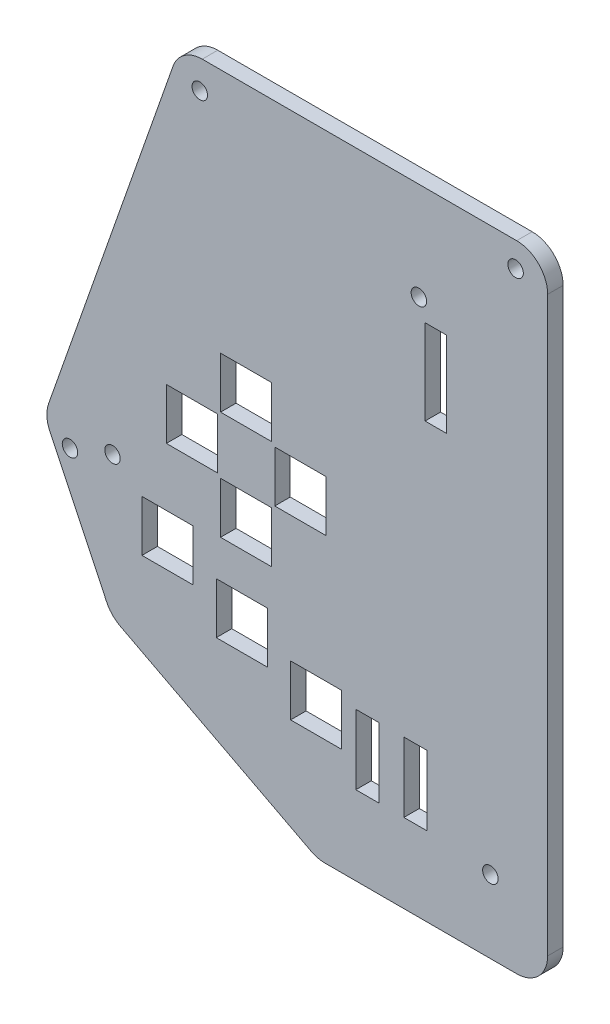
SolidWorks part; units mm, degrees
ref_plane "Front Plane" through (0, 0, 0) normal (0, 0, 1) x (1, 0, 0)
ref_plane "Top Plane" through (0, 0, 0) normal (0, 1, 0) x (1, 0, 0)
ref_plane "Right Plane" through (0, 0, 0) normal (1, 0, 0) x (0, 0, -1)
sketch "Sketch1" plane through (0, 0, 0) normal (0, 0, 1) x (1, 0, 0)
  line L6 (-20.066, -57.15) -> (46.99, -57.15) construction
  line L7 (-12.446, -73.152) -> (46.99, -73.152) construction
  line L8 (-3.3141, 6.35) -> (48.26, 6.35)
  line L9 (53.34, 1.27) -> (53.34, -92.71)
  line L10 (48.26, -97.79) -> (16.847, -97.79)
  line L16 (-8.1072, 2.9529) -> (-28.5162, -55.1739)
  line L18 (-20.066, -57.15) -> (-29.21, -57.15) construction
  line L26 (0, 0) -> (46.99, 0) construction
  line L27 (46.99, 0) -> (46.99, -88.9) construction
  line L28 (46.99, -88.9) -> (17.78, -88.9) construction
  line L29 (17.78, -88.9) -> (-12.446, -73.152) construction
  line L30 (-12.446, -73.152) -> (-20.066, -57.15) construction
  line L31 (-20.066, -57.15) -> (0, 0) construction
  line L32 (46.99, -57.15) -> (46.99, -88.9) construction
  line L33 (17.78, -88.9) -> (15.603, -97.79) construction
  line L34 (-12.446, -73.152) -> (-17.9301, -78.4424) construction
  line L35 (14.4997, -97.2152) -> (-16.7505, -80.9336)
  line L36 (-28.3096, -59.0409) -> (-18.9898, -78.6124)
  arc A0 (53.34, -92.71) -> (48.26, -97.79) centre (48.26, -92.71) cw
  arc A1 (14.4997, -97.2152) -> (16.847, -97.79) centre (16.847, -92.71) ccw
  arc A2 (-16.7505, -80.9336) -> (-18.9898, -78.6124) centre (-14.4033, -76.4284) cw
  arc A3 (-28.5162, -55.1739) -> (-28.3096, -59.0409) centre (-23.723, -56.8568) ccw
  arc A4 (-8.1072, 2.9529) -> (-3.3141, 6.35) centre (-3.3141, 1.27) cw
  arc A5 (48.26, 6.35) -> (53.34, 1.27) centre (48.26, 1.27) cw
  point P13 (53.34, -97.79)
  point P32 (53.34, 6.35)
  dimension "D8" = 5.08
  dimension "D1" = 88.9
  dimension "D2" = 29.21
  dimension "D3" = 59.436
  dimension "D4" = 67.056
  dimension "D5" = 104.14
  dimension "D6" = 82.55
  dimension "D7" = 46.99
  dimension "D13" = 103.76
  dimension "D17" = 108.51
sketch "Sketch3" plane through (0, 0, 0) normal (0, 0, 1) x (1, 0, 0)
  line L6 (-20.066, -57.15) -> (46.99, -57.15) construction
  line L7 (-12.446, -73.152) -> (46.99, -73.152) construction
  line L8 (0, 0) -> (46.99, 0) construction
  line L9 (46.99, 0) -> (46.99, -88.9) construction
  line L10 (46.99, -88.9) -> (17.78, -88.9) construction
  line L11 (17.78, -88.9) -> (-12.446, -73.152) construction
  line L12 (-12.446, -73.152) -> (-20.066, -57.15) construction
  line L13 (-20.066, -57.15) -> (0, 0) construction
  line L14 (3.8784, -55.88) -> (3.8784, -38.1) construction
  circle A0 centre (3.8784, -38.1) radius 5.08
  circle A1 centre (-5.0116, -46.99) radius 5.08
  circle A2 centre (3.8784, -55.88) radius 5.08
  circle A3 centre (12.7684, -46.99) radius 5.08
  circle A4 centre (-9.144, -65.024) radius 5.08
  circle A5 centre (3.048, -70.612) radius 5.08
  circle A6 centre (15.24, -76.2) radius 5.08
  dimension "D7" = 10.16
  dimension "D1" = 43.1116
  dimension "D2" = 8.89
  dimension "D3" = 8.89
  dimension "D4" = 46.99
  dimension "D5" = 8.89
  dimension "D6" = 8.89
  dimension "D8" = 12.192
  dimension "D9" = 5.588
  dimension "D10" = 5.588
  dimension "D11" = 12.192
  dimension "D12" = 43.942
  dimension "D13" = 70.612
sketch "Sketch10" plane through (0, 0, 0) normal (0, 0, 1) x (1, 0, 0)
  line L1 (53.34, 1.27) -> (53.34, -92.71)
  line L6 (48.26, -97.79) -> (16.847, -97.79)
  line L16 (-8.1072, 2.9529) -> (-28.5162, -55.1739)
  line L19 (53.34, 1.27) -> (53.34, -92.71) construction
  line L21 (-8.1072, 2.9529) -> (-28.5162, -55.1739) construction
  line L24 (14.4997, -97.2152) -> (-16.7505, -80.9336)
  line L25 (-18.9898, -78.6124) -> (-28.3096, -59.0409)
  line L26 (-3.3141, 6.35) -> (48.26, 6.35)
  arc A0 (-18.9898, -78.6124) -> (-16.7505, -80.9336) centre (-14.4033, -76.4284) ccw
  arc A1 (16.847, -97.79) -> (14.4997, -97.2152) centre (16.847, -92.71) cw
  arc A2 (-28.5162, -55.1739) -> (-28.3096, -59.0409) centre (-23.723, -56.8568) ccw
  arc A3 (53.34, -92.71) -> (48.26, -97.79) centre (48.26, -92.71) cw
  arc A4 (-8.1072, 2.9529) -> (-3.3141, 6.35) centre (-3.3141, 1.27) cw
  arc A5 (48.26, 6.35) -> (53.34, 1.27) centre (48.26, 1.27) cw
  point P13 (15.603, -97.79)
  point P17 (-29.21, -57.15)
  point P20 (53.34, -97.79)
  dimension "D1" = 5.08
extrude "Boss-Extrude1" add sketch "Sketch10" along normal blind 2.54
sketch "Sketch11" plane through (0, 0, 2.54) normal (0, 0, 1) x (1, 0, 0)
  line L0 (46.99, -88.9) -> (17.78, -88.9) construction
  line L5 (33.561, -73.406) -> (29.751, -73.406)
  line L6 (33.561, -73.406) -> (33.561, -84.836)
  line L11 (33.561, -84.836) -> (29.751, -84.836)
  line L12 (29.751, -73.406) -> (29.751, -84.836)
  line L18 (46.99, 0) -> (46.99, -88.9) construction
  line L23 (25.687, -73.406) -> (21.877, -73.406)
  line L24 (25.687, -73.406) -> (25.687, -84.836)
  line L29 (25.687, -84.836) -> (21.877, -84.836)
  line L30 (21.877, -73.406) -> (21.877, -84.836)
  line L42 (8.0694, -51.689) -> (-0.3126, -51.689)
  line L43 (8.0694, -51.689) -> (8.0694, -60.071)
  line L44 (8.0694, -60.071) -> (-0.3126, -60.071)
  line L45 (-0.3126, -51.689) -> (-0.3126, -60.071)
  line L46 (-0.8206, -42.799) -> (-9.2026, -42.799)
  line L47 (-0.8206, -42.799) -> (-0.8206, -51.181)
  line L48 (-0.8206, -51.181) -> (-9.2026, -51.181)
  line L49 (-9.2026, -42.799) -> (-9.2026, -51.181)
  line L52 (8.0694, -42.291) -> (-0.3126, -42.291)
  line L53 (-0.3126, -33.909) -> (-0.3126, -42.291)
  line L54 (16.9594, -42.799) -> (8.5774, -42.799)
  line L55 (16.9594, -42.799) -> (16.9594, -51.181)
  line L56 (16.9594, -51.181) -> (8.5774, -51.181)
  line L57 (8.5774, -42.799) -> (8.5774, -51.181)
  line L58 (-0.3126, -33.909) -> (8.0694, -33.909)
  line L59 (8.0694, -33.909) -> (8.0694, -42.291)
  line L60 (3.8784, -51.689) -> (3.8784, -60.071) construction
  line L61 (-0.3126, -55.88) -> (8.0694, -55.88) construction
  line L62 (-5.0116, -51.181) -> (-5.0116, -42.799) construction
  line L63 (-9.2026, -46.99) -> (-0.8206, -46.99) construction
  line L64 (12.7684, -42.799) -> (12.7684, -51.181) construction
  line L65 (8.5774, -46.99) -> (16.9594, -46.99) construction
  line L66 (3.8784, -33.909) -> (3.8784, -42.291) construction
  line L67 (-0.3126, -38.1) -> (8.0694, -38.1) construction
  line L68 (-4.826, -60.706) -> (-4.826, -69.088)
  line L69 (-13.208, -65.024) -> (-5.08, -65.024) construction
  line L70 (-9.144, -60.96) -> (-9.144, -69.088) construction
  line L71 (-4.826, -69.088) -> (-13.208, -69.088)
  line L72 (-13.208, -60.706) -> (-13.208, -69.088)
  line L73 (-4.826, -60.706) -> (-13.208, -60.706)
  line L74 (7.366, -66.294) -> (7.366, -74.676)
  line L75 (-1.016, -70.612) -> (7.112, -70.612) construction
  line L76 (3.048, -66.548) -> (3.048, -74.676) construction
  line L77 (7.366, -74.676) -> (-1.016, -74.676)
  line L78 (-1.016, -66.294) -> (-1.016, -74.676)
  line L79 (7.366, -66.294) -> (-1.016, -66.294)
  line L80 (19.558, -71.882) -> (19.558, -80.264)
  line L81 (11.176, -76.2) -> (19.304, -76.2) construction
  line L82 (15.24, -72.136) -> (15.24, -80.264) construction
  line L83 (19.558, -80.264) -> (11.176, -80.264)
  line L84 (11.176, -71.882) -> (11.176, -80.264)
  line L85 (19.558, -71.882) -> (11.176, -71.882)
  dimension "D1" = 4.064
  dimension "D3" = 13.429
  dimension "D4" = 11.43
  dimension "D5" = 3.81
  dimension "D6" = 4.064
  dimension "D7" = 11.43
  dimension "D8" = 4.064
  dimension "D9" = 4.572
  dimension "D10" = 2.319
  dimension "D11" = 8.382
  dimension "D12" = 5.588
  dimension "D13" = 3.81
  dimension "D14" = 3.81
  dimension "D15" = 3.81
  dimension "D16" = 5.588
  dimension "D17" = 8.89
  dimension "D18" = 8.382
  dimension "D21" = 8.382
  dimension "D22" = 8.382
extrude "Cut-Extrude1" cut sketch "Sketch11" against normal through all both and the other way through all
sketch "Sketch12" plane through (0, 0, 0) normal (0, 0, -1) x (-1, 0, 0)
  line L0 (20.066, -57.15) -> (-46.99, -57.15) construction
  line L2 (-46.99, 0) -> (-46.99, -88.9) construction
  line L5 (18.034, -57.15) -> (20.066, -57.15) construction
  line L10 (-46.99, -88.9) -> (-17.78, -88.9) construction
  circle A2 centre (18.034, -57.15) radius 1.27
  circle A3 centre (-43.942, -85.852) radius 1.27
  dimension "D1" = 2.54
  dimension "D6" = 2.032
  dimension "D2" = 2.54
  dimension "D11" = 3.048
  dimension "D12" = 3.048
extrude "Cut-Extrude2" cut sketch "Sketch12" against normal through all both and the other way through all
sketch "Sketch13" plane through (0, 0, 0) normal (0, 0, -1) x (-1, 0, 0)
  line L0 (28.3096, -59.0409) -> (18.9898, -78.6124) construction
  line L1 (8.1072, 2.9529) -> (28.5162, -55.1739) construction
  line L2 (3.3141, 6.35) -> (-48.26, 6.35) construction
  line L4 (-53.34, 1.27) -> (-53.34, -92.71) construction
  circle A1 centre (25.0123, -59.762) radius 1.27
  circle A4 centre (-48.0822, 2.286) radius 1.27
  circle A5 centre (3.7187, 1.651) radius 1.27
  dimension "D1" = 2.54
  dimension "D2" = 4.826
  dimension "D4" = 4.064
  dimension "D3" = 2.667
  dimension "D5" = 5.2578
  dimension "D6" = 4.699
  dimension "D7" = 4.572
extrude "Cut-Extrude3" cut sketch "Sketch13" against normal through all both and the other way through all
sketch "Sketch14" plane through (0, 0, 0) normal (0, 0, -1) x (-1, 0, 0)
  line L0 (-36.7885, -26.7831) -> (-33.2325, -26.7831)
  line L1 (-36.7885, -12.8131) -> (-36.7885, -26.7831)
  line L2 (-33.2325, -12.8131) -> (-36.7885, -12.8131)
  line L3 (-33.2325, -12.8131) -> (-33.2325, -26.7831)
  line L4 (-53.34, 1.27) -> (-53.34, -92.71) construction
  line L5 (3.3141, 6.35) -> (-48.26, 6.35) construction
  dimension "D1" = 16.5515
  dimension "D2" = 3.556
  dimension "D3" = 19.1631
  dimension "D4" = 13.97
extrude "Cut-Extrude4" cut sketch "Sketch14" against normal through all both and the other way through all
sketch "Sketch16" plane through (0, 0, 0) normal (0, 0, -1) x (-1, 0, 0)
  line L0 (3.3141, 6.35) -> (-48.26, 6.35) construction
  line L1 (-53.34, 1.27) -> (-53.34, -92.71) construction
  circle A0 centre (-32.219, -9.6761) radius 1.27
  dimension "D1" = 16.0261
  dimension "D2" = 2.54
  dimension "D3" = 21.121
extrude "Cut-Extrude5" cut sketch "Sketch16" against normal through all both and the other way through all
